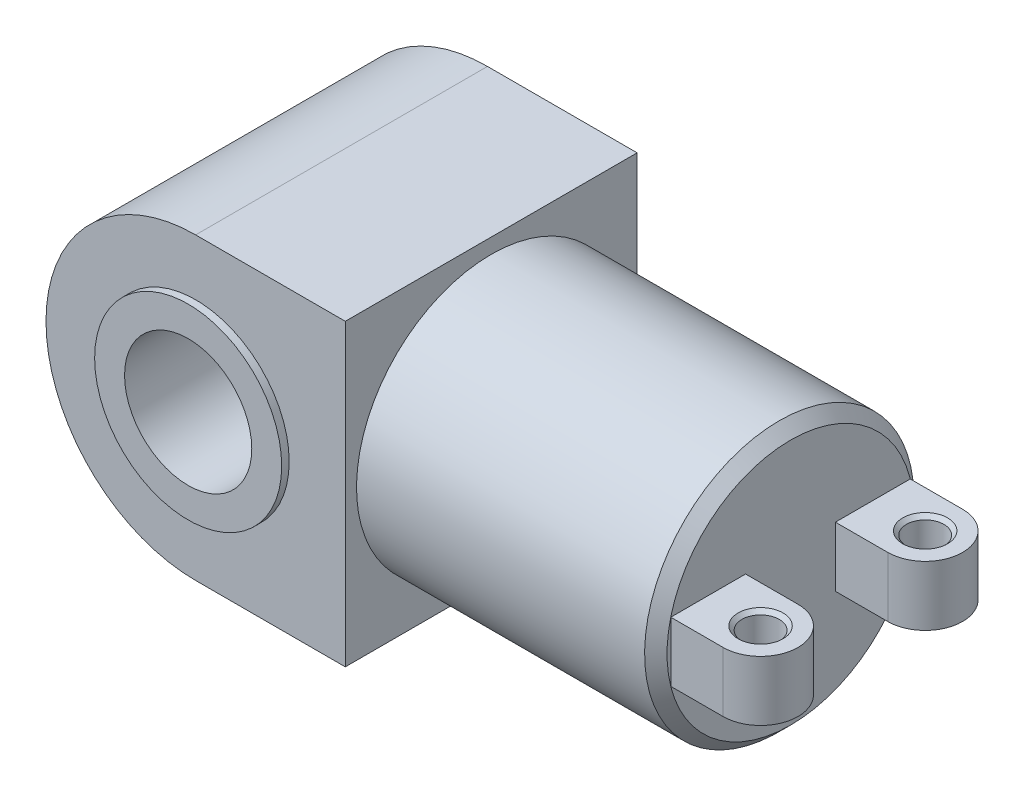
SolidWorks part; units mm, degrees
material "Balsa"
ref_plane "Front Plane" through (0, 0, 0) normal (0, 0, 1) x (1, 0, 0)
ref_plane "Top Plane" through (0, 0, 0) normal (0, 1, 0) x (1, 0, 0)
ref_plane "Right Plane" through (0, 0, 0) normal (1, 0, 0) x (0, 0, -1)
sketch "Sketch1" plane through (0, 0, 0) normal (0, 0, 1) x (1, 0, 0)
  line L0 (0, 0) -> (100, 0) construction
  line L1 (100, 100) -> (100, -100)
  line L2 (100, 100) -> (0, 100)
  line L3 (0, -100) -> (100, -100)
  circle A0 centre (0, 0) radius 42.5
  arc A1 (0, 100) -> (0, -100) centre (0, 0) ccw
  point P7 (100, 0)
  dimension "D1" = 85
  dimension "D2" = 200
  dimension "D3" = 200
  dimension "D4" = 100
extrude "Boss-Extrude1" add sketch "Sketch1" along normal mid plane 195
sketch "Sketch2" plane through (0, 0, -97.5) normal (0, 0, -1) x (-1, 0, 0)
  circle A0 centre (0, 0) radius 42.5 construction
  circle A1 centre (0, 0) radius 42.5
  circle A2 centre (0, 0) radius 62.5
  dimension "D1" = 125
extrude "Boss-Extrude2" add sketch "Sketch2" along normal blind 5
sketch "Sketch3" plane through (0, 0, 97.5) normal (0, 0, 1) x (1, 0, 0)
  circle A0 centre (0, 0) radius 42.5 construction
  circle A1 centre (0, 0) radius 62.5
  circle A2 centre (0, 0) radius 62.5
  circle A3 centre (0, 0) radius 42.5
  dimension "D1" = 0
extrude "Boss-Extrude3" add sketch "Sketch3" along normal blind 5
sketch "Sketch4" plane through (100, 0, 0) normal (1, 0, 0) x (0, 0, -1)
  circle A0 centre (0, 0) radius 90
  dimension "D1" = 180
extrude "Boss-Extrude4" add sketch "Sketch4" along normal blind 200
sketch "Sketch6" plane through (0, 0, 0) normal (0, 1, 0) x (1, 0, 0)
  line L1 (300, -80) -> (335, -80)
  line L2 (300, -80) -> (300, -30)
  line L3 (300, -30) -> (335, -30)
  line L5 (300, 80) -> (335, 80)
  line L6 (300, 80) -> (300, 30)
  line L7 (300, 30) -> (335, 30)
  line L8 (300, 90) -> (100, 90) construction
  line L9 (100, -90) -> (300, -90) construction
  line L10 (300, -90) -> (300, 90) construction
  line L11 (335, 55) -> (335, -55) construction
  arc A0 (335, -80) -> (335, -30) centre (335, -55) ccw
  arc A1 (335, 30) -> (335, 80) centre (335, 55) ccw
  circle A2 centre (335, -55) radius 12.5
  circle A3 centre (335, 55) radius 12.5
  dimension "D2" = 25
  dimension "D9" = 35
  dimension "D1" = 35
  dimension "D3" = 35
  dimension "D4" = 35
  dimension "D5" = 25
  dimension "D6" = 25
  dimension "D7" = 10
  dimension "D8" = 10
extrude "Boss-Extrude5" add sketch "Sketch6" along normal mid plane 40
chamfer "Chamfer1" distance 7.5 angle 45 1 edges at (300, 90, 0)
chamfer "Chamfer2" distance 2.5 angle 45 4 edges at (335, -20, 67.5) (335, 20, 67.5) (335, -20, -42.5) (335, 20, -42.5)
